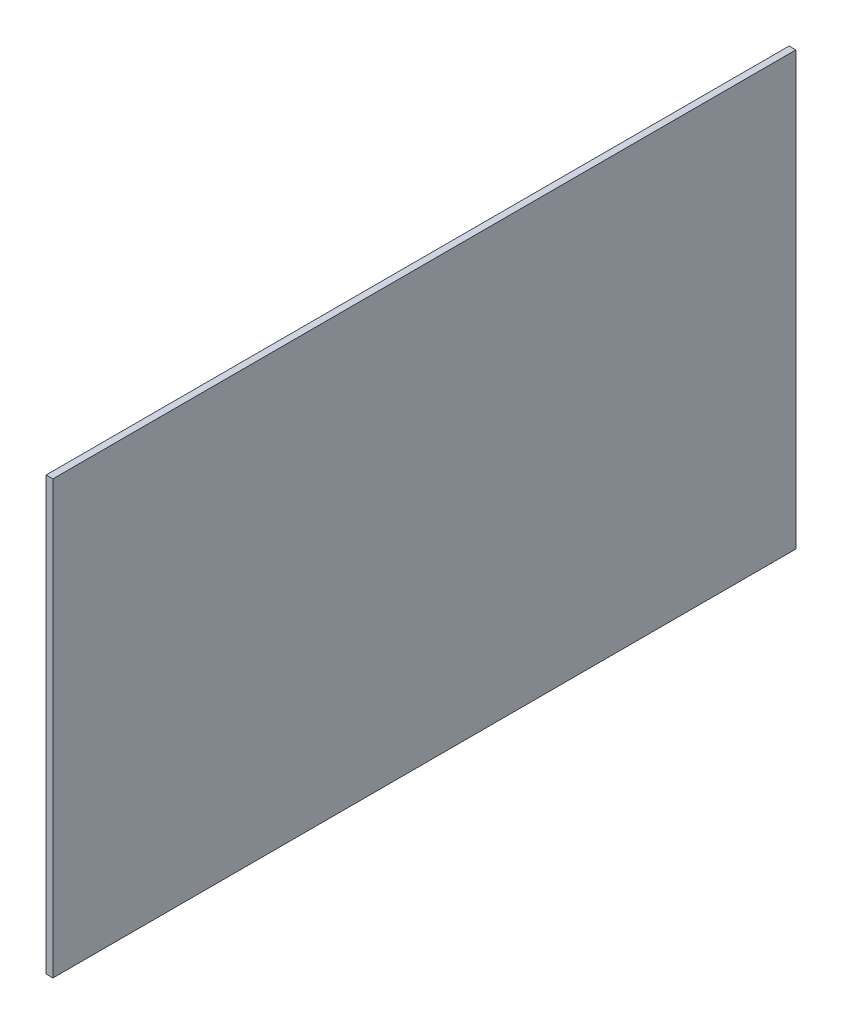
SolidWorks part; units mm, degrees
material "Acrylic (Medium-high impact)"
ref_plane "Front Plane" through (0, 0, 0) normal (0, 0, 1) x (1, 0, 0)
ref_plane "Top Plane" through (0, 0, 0) normal (0, 1, 0) x (1, 0, 0)
ref_plane "Right Plane" through (0, 0, 0) normal (1, 0, 0) x (0, 0, -1)
sketch "Sketch1" plane through (0, 0, 0) normal (1, 0, 0) x (0, 0, -1)
  line L1 (349.25, -203.2) -> (-349.25, -203.2)
  line L2 (349.25, -203.2) -> (349.25, 203.2)
  line L3 (349.25, 203.2) -> (-349.25, 203.2)
  line L4 (-349.25, -203.2) -> (-349.25, 203.2)
  line L5 (349.25, -203.2) -> (-349.25, 203.2) construction
  line L6 (349.25, 203.2) -> (-349.25, -203.2) construction
  point P0 (0, 0)
  dimension "D1" = 698.5
  dimension "D2" = 406.4
extrude "Boss-Extrude1" add sketch "Sketch1" along normal blind 6.35
